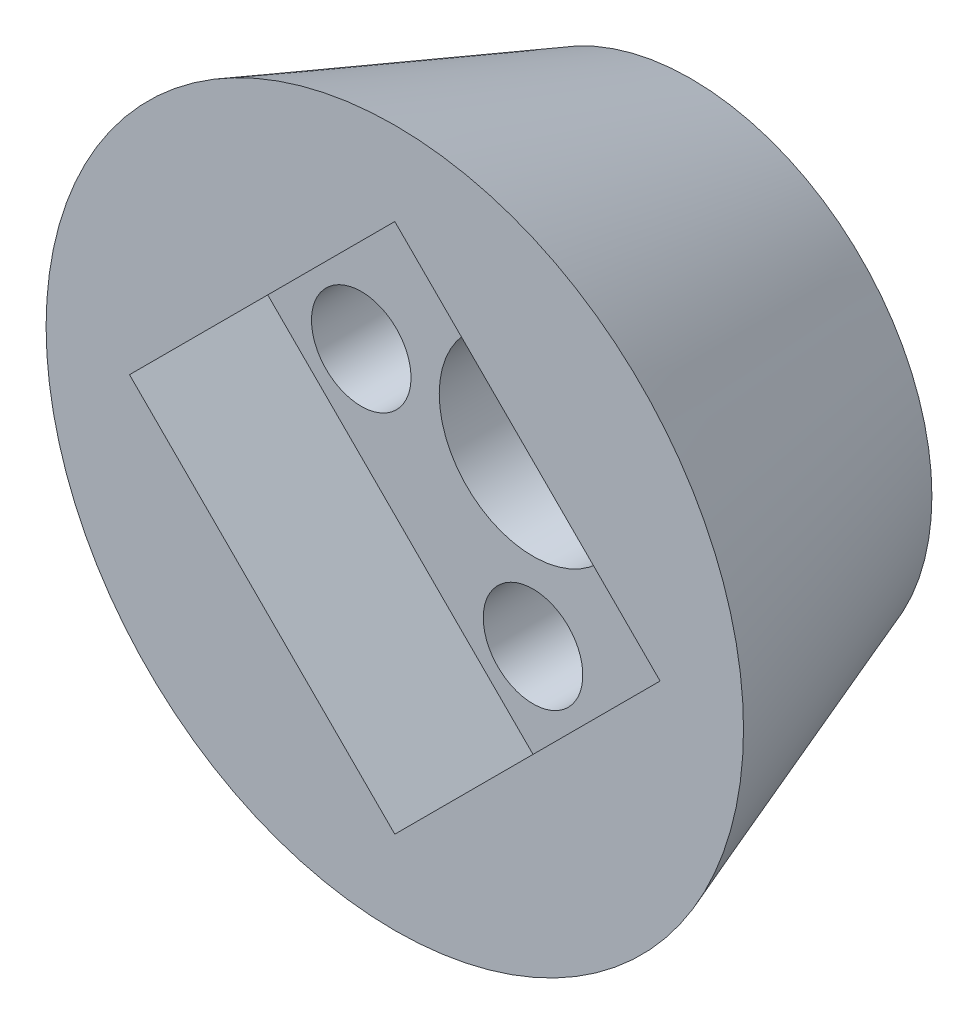
SolidWorks part; units mm, degrees
ref_plane "Front" through (0, 0, 0) normal (0, 0, 1) x (1, 0, 0)
ref_plane "Top" through (0, 0, 0) normal (0, 1, 0) x (1, 0, 0)
ref_plane "Right" through (0, 0, 0) normal (1, 0, 0) x (0, 0, -1)
sketch "GearFaceProfile" plane through (0, 0, 0) normal (0, 0, 1) x (1, 0, 0)
  circle A0 centre (0, 0) radius 12.2
  dimension "D1" = 24.4
extrude "GearFaceExtrude" add sketch "GearFaceProfile" along normal blind 15 draft 20 draft outward yes
sketch "CenterHoleProfile" plane through (0, 0, 0) normal (0, 0, -1) x (-1, 0, 0)
  circle A0 centre (0, 0) radius 4.75
  dimension "D1" = 9.5
extrude "CenterHoleCut" cut sketch "CenterHoleProfile" against normal through all
sketch "ScrewHoleProfile" plane through (0, 0, 0) normal (0, 0, -1) x (-1, 0, 0)
  line L0 (0, 0) -> (0, 8.7) construction
  line L1 (0, 0) -> (8.7, 0) construction
  line L2 (0, 0) -> (0, -8.7) construction
  line L3 (0, 0) -> (-8.7, 0) construction
  circle A2 centre (0, 8.7) radius 2.52
  circle A3 centre (8.7, 0) radius 2.52
  circle A4 centre (0, -8.7) radius 2.52
  circle A5 centre (-8.7, 0) radius 2.52
  dimension "D5" = 5.04
  dimension "D6" = 5.04
  dimension "D7" = 5.04
  dimension "D8" = 5.04
  dimension "D1" = 8.7
  dimension "D2" = 8.7
  dimension "D3" = 8.7
  dimension "D4" = 8.7
extrude "ScrewHoleCut" cut sketch "ScrewHoleProfile" against normal through all
sketch "ShaftCollarAttachmentProfile" plane through (0, 0, 15) normal (0, 0, 1) x (1, 0, 0)
  line L0 (0, 0) -> (0, 13.435) construction
  line L1 (0, 0) -> (13.435, 0) construction
  line L2 (0, 13.435) -> (13.435, 0)
  line L3 (13.435, 0) -> (0, -13.435)
  line L4 (0, -13.435) -> (-13.435, 0)
  line L5 (-13.435, 0) -> (0, 13.435)
  dimension "D1" = 19
  dimension "D2" = 19
extrude "ShaftCollarDockingCut" cut sketch "ShaftCollarAttachmentProfile" against normal blind 7
equation "\"ScrewHole-Center\"=8.70mm"
equation "\"ScrewHoleDiameter\"=5.04mm"
equation "\"CenterHoleDiameter\"=9.50mm"
equation "\"GearFaceDiameter\"=24.40mm"
equation "\"D1@GearFaceProfile\"= \"GearFaceDiameter\""
equation "\"D1@CenterHoleProfile\"= \"CenterHoleDiameter\""
equation "\"D4@ScrewHoleProfile\"= \"ScrewHole-Center\""
equation "\"D1@ScrewHoleProfile\"= \"ScrewHole-Center\""
equation "\"D2@ScrewHoleProfile\"= \"ScrewHole-Center\""
equation "\"D3@ScrewHoleProfile\"= \"ScrewHole-Center\""
equation "\"D5@ScrewHoleProfile\"= \"ScrewHoleDiameter\""
equation "\"D6@ScrewHoleProfile\"= \"ScrewHoleDiameter\""
equation "\"D8@ScrewHoleProfile\"= \"ScrewHoleDiameter\""
equation "\"D7@ScrewHoleProfile\"= \"ScrewHoleDiameter\""
equation "\"CylinderLength\"=15.00mm"
equation "\"ShaftCollarSideLength\"=19.00mm"
equation "\"D1@ShaftCollarAttachmentProfile\"= \"ShaftCollarSideLength\""
equation "\"D2@ShaftCollarAttachmentProfile\"= \"ShaftCollarSideLength\""
equation "\"ShaftCollarDockingDepth\"=7.00mm"
